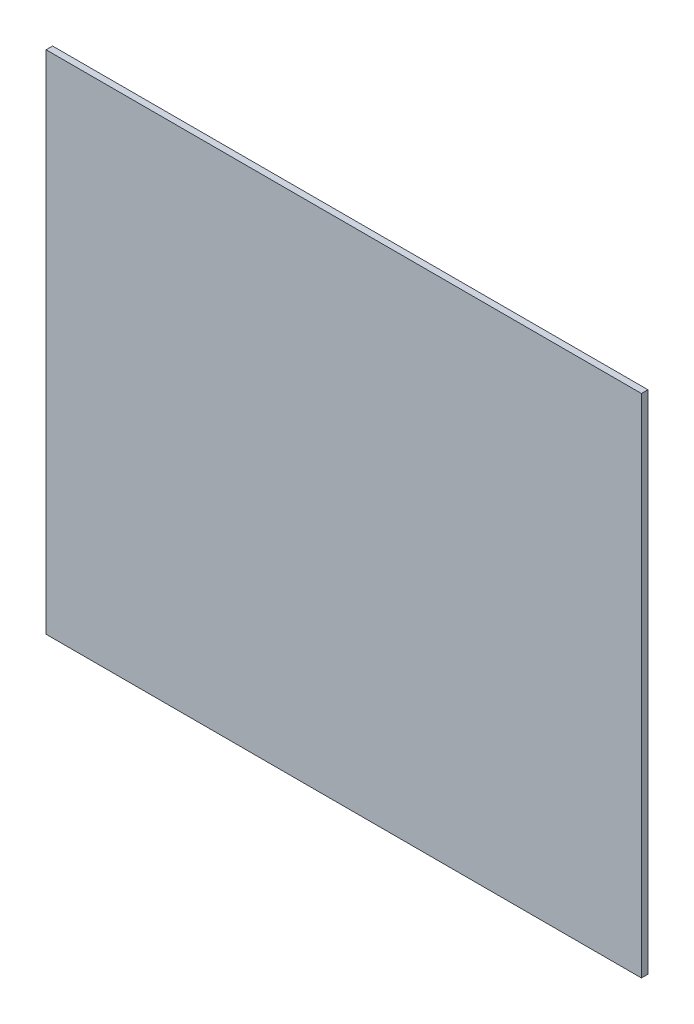
SolidWorks part; units mm, degrees
ref_plane "Front" through (0, 0, 0) normal (0, 0, 1) x (1, 0, 0)
ref_plane "Top" through (0, 0, 0) normal (0, 1, 0) x (1, 0, 0)
ref_plane "Right" through (0, 0, 0) normal (1, 0, 0) x (0, 0, -1)
sketch "Sketch1" plane through (0, 0, 0) normal (0, 0, 1) x (1, 0, 0)
  line L1 (-47.1467, 40.0229) -> (44.5562, 40.0229)
  line L2 (-47.1467, 40.0229) -> (-47.1467, -37.9505)
  line L3 (-47.1467, -37.9505) -> (44.5562, -37.9505)
  line L4 (44.5562, 40.0229) -> (44.5562, -37.9505)
extrude "Boss-Extrude1" add sketch "Sketch1" along normal blind 1
